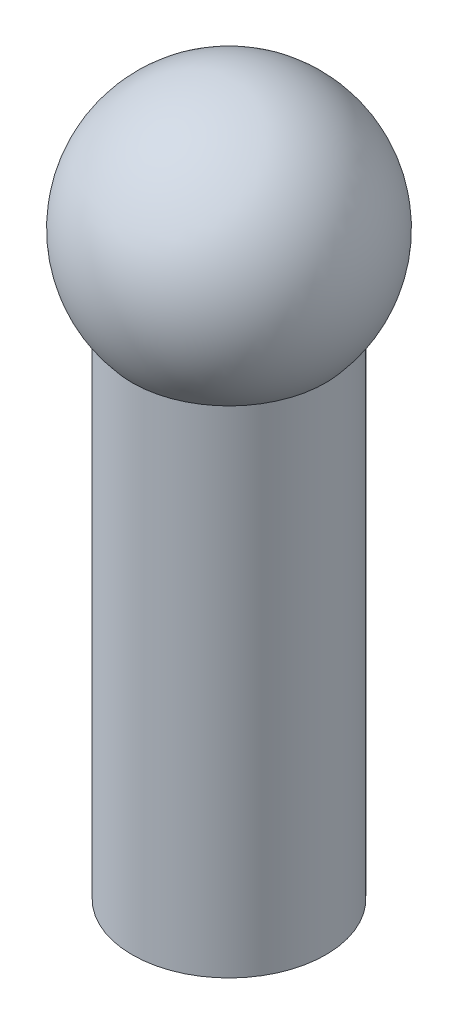
SolidWorks part; units mm, degrees
ref_plane "Front Plane" through (0, 0, 0) normal (0, 0, 1) x (1, 0, 0)
ref_plane "Top Plane" through (0, 0, 0) normal (0, 1, 0) x (1, 0, 0)
ref_plane "Right Plane" through (0, 0, 0) normal (1, 0, 0) x (0, 0, -1)
sketch "Sketch1" plane through (0, 0, 0) normal (0, 1, 0) x (1, 0, 0)
  circle A0 centre (0, 0) radius 1.5
  dimension "D1" = 3
extrude "Boss-Extrude1" add sketch "Sketch1" along normal blind 9
sketch "Sketch2" plane through (0, 9, 0) normal (0, 1, 0) x (1, 0, 0)
  line L0 (2, 0) -> (-2, 0)
  arc A0 (2, 0) -> (-2, 0) centre (0, 0) ccw
  dimension "D1" = 4
revolve "Revolve1" add sketch "Sketch2" angle 360 about L0
